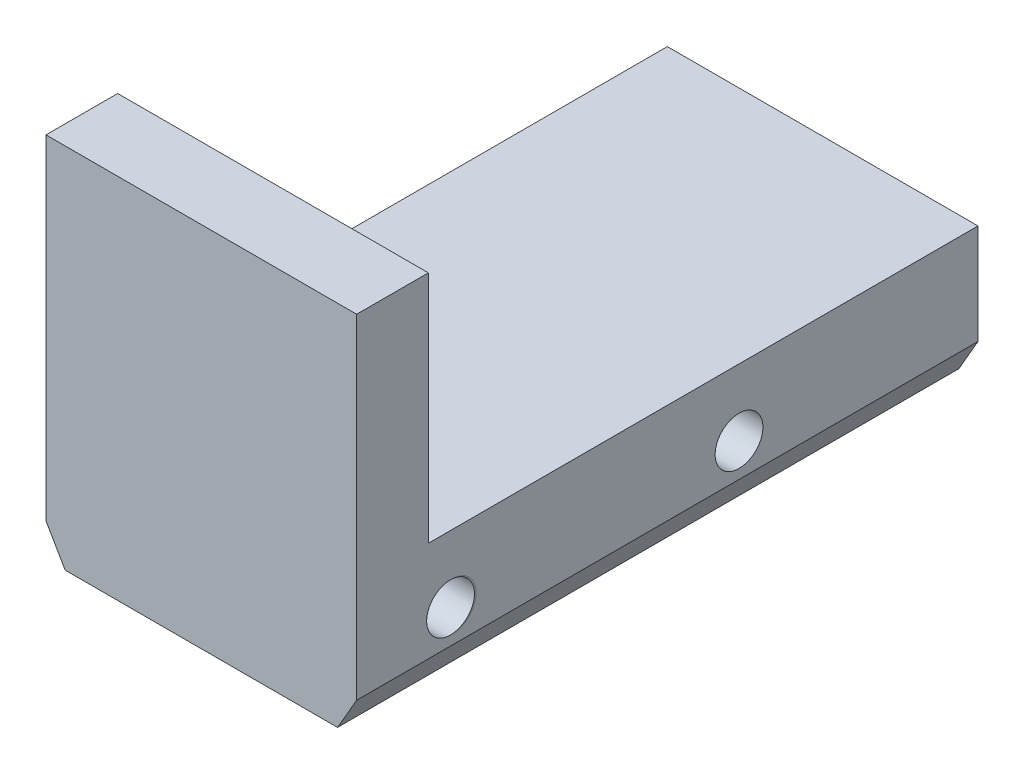
SolidWorks part; units mm, degrees
material "ﾒﾗﾐﾝ樹脂"
ref_plane "正面" through (0, 0, 0) normal (0, 0, 1) x (1, 0, 0)
ref_plane "平面" through (0, 0, 0) normal (0, 1, 0) x (1, 0, 0)
ref_plane "右側面" through (0, 0, 0) normal (1, 0, 0) x (0, 0, -1)
sketch "ｽｹｯﾁ1" plane through (0, 0, 0) normal (0, 1, 0) x (1, 0, 0)
  line L0 (0, 0) -> (13, 0)
  line L1 (13, 0) -> (13, 26)
  line L2 (13, 26) -> (0, 26)
  line L3 (0, 26) -> (0, 0)
extrude "ﾎﾞｽ - 押し出し1" add sketch "ｽｹｯﾁ1" along normal blind 5.5737
sketch "ｽｹｯﾁ2" plane through (0, 5.5737, 0) normal (0, 1, 0) x (1, 0, 0)
  line L0 (0, 0) -> (0, 3)
  line L1 (0, 26) -> (0, 0) construction
  line L2 (0, 3) -> (13, 3)
  line L3 (13, 0) -> (13, 26) construction
  line L4 (13, 3) -> (13, 0)
  line L5 (13, 0) -> (0, 0)
extrude "ﾎﾞｽ - 押し出し2" add sketch "ｽｹｯﾁ2" along normal blind 9.8
sketch "ｽｹｯﾁ4" plane through (0, 0, 0) normal (-1, 0, 0) x (0, 0, 1)
  line L0 (-26, 0) -> (-26, 2.7869)
  line L1 (-26, 5.5737) -> (-26, 0) construction
  circle A0 centre (-16, 2.7869) radius 1
  circle A1 centre (-4, 2.7869) radius 1
extrude "ｶｯﾄ - 押し出し1" cut sketch "ｽｹｯﾁ4" against normal through all contours A0 | A1
chamfer "面取り2" distance 0.8 angle 60 2 edges at (13, 0, -13) (0, 0, -13)
sketch "ｽｹｯﾁ5" plane through (0, 0, 0) normal (-1, 0, 0) x (0, 0, 1)
  circle A0 centre (-4, 2.7869) radius 1
extrude "ﾎﾞｽ - 押し出し3" add sketch "ｽｹｯﾁ5" against normal through all
sketch "ｽｹｯﾁ6" plane through (0, 0, 0) normal (-1, 0, 0) x (0, 0, 1)
  circle A0 centre (-3.9284, 2.7869) radius 1
extrude "ｶｯﾄ - 押し出し2" cut sketch "ｽｹｯﾁ6" against normal through all
